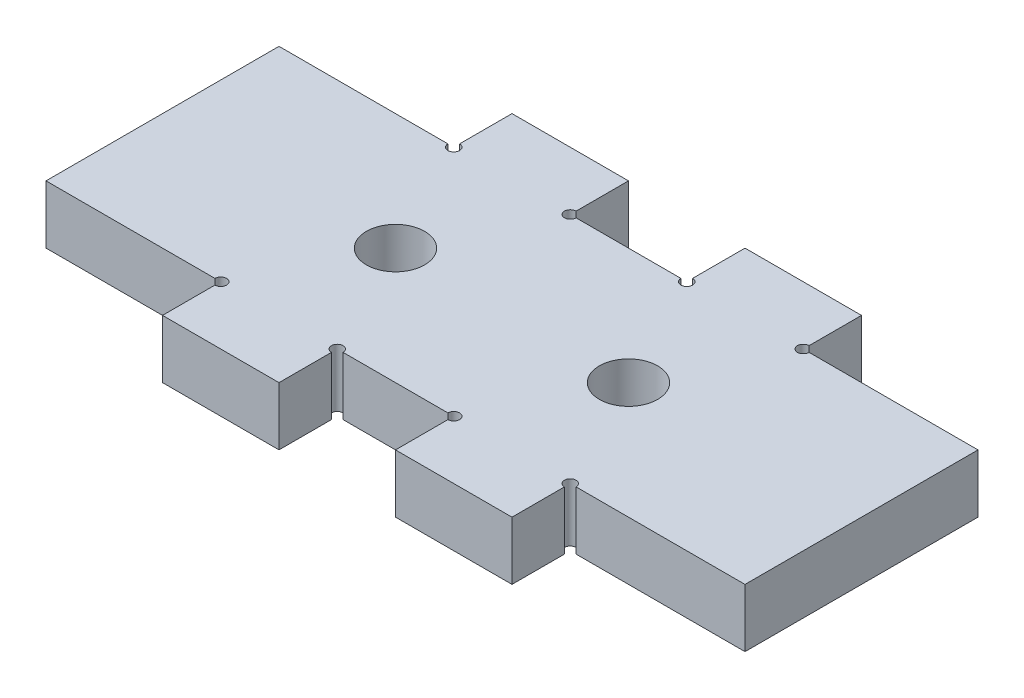
SolidWorks part; units mm, degrees
material "Acrylic (Medium-high impact)"
ref_plane "Front Plane" through (0, 0, 0) normal (0, 0, 1) x (1, 0, 0)
ref_plane "Top Plane" through (0, 0, 0) normal (0, 1, 0) x (1, 0, 0)
ref_plane "Right Plane" through (0, 0, 0) normal (1, 0, 0) x (0, 0, -1)
sketch "Sketch1" plane through (0, 0, 0) normal (0, 1, 0) x (1, 0, 0)
  line L0 (-19.05, 12.7) -> (-19.05, 19.05)
  line L1 (-38.1, 12.7) -> (-19.05, 12.7)
  line L2 (-38.1, 12.7) -> (-38.1, -12.7)
  line L3 (-38.1, -12.7) -> (-19.05, -12.7)
  line L4 (38.1, 12.7) -> (38.1, -12.7)
  line L5 (-38.1, 12.7) -> (38.1, -12.7) construction
  line L6 (-38.1, -12.7) -> (38.1, 12.7) construction
  line L7 (-19.05, 19.05) -> (-6.35, 19.05)
  line L8 (-6.35, 19.05) -> (-6.35, 12.7)
  line L9 (-6.35, 12.7) -> (6.35, 12.7)
  line L10 (0, -4.7893) -> (0, 19.05) construction
  line L11 (6.35, 19.05) -> (6.35, 12.7)
  line L12 (19.05, 19.05) -> (6.35, 19.05)
  line L13 (19.05, 12.7) -> (19.05, 19.05)
  line L14 (-8.6907, 0) -> (8.2657, 0) construction
  line L15 (-6.35, -19.05) -> (-6.35, -12.7)
  line L16 (-19.05, -19.05) -> (-6.35, -19.05)
  line L17 (-19.05, -12.7) -> (-19.05, -19.05)
  line L18 (19.05, -12.7) -> (19.05, -19.05)
  line L19 (19.05, -19.05) -> (6.35, -19.05)
  line L20 (6.35, -19.05) -> (6.35, -12.7)
  line L21 (19.05, 12.7) -> (38.1, 12.7)
  line L22 (19.05, -12.7) -> (38.1, -12.7)
  line L23 (-6.35, -12.7) -> (6.35, -12.7)
  point P0 (0, 0)
  dimension "D1" = 25.4
  dimension "D2" = 6.35
  dimension "D3" = 12.7
  dimension "D4" = 12.7
  dimension "D5" = 19.05
extrude "Boss-Extrude1" add sketch "Sketch1" along normal blind 6.35
sketch "Sketch2" plane through (0, 6.35, 0) normal (0, 1, 0) x (1, 0, 0)
  line L0 (-6.35, 19.05) -> (-19.05, 19.05) construction
  line L1 (19.05, 19.05) -> (6.35, 19.05) construction
  circle A0 centre (-12.7, 0) radius 3.175
  circle A1 centre (12.7, 0) radius 3.175
  point P7 (-12.7, 19.05)
  point P10 (12.7, 19.05)
  dimension "D1" = 6.35
  dimension "D2" = 6.35
extrude "Cut-Extrude1" cut sketch "Sketch2" against normal up to next
sketch "Sketch3" plane through (0, 6.35, 0) normal (0, 1, 0) x (1, 0, 0)
  point P0 (-19.05, 12.7)
  point P1 (-6.35, 12.7)
  point P3 (6.35, 12.7)
  point P5 (19.05, 12.7)
  point P7 (19.05, -12.7)
  point P9 (6.35, -12.7)
  point P11 (-6.35, -12.7)
  point P13 (-19.05, -12.7)
sketch "Sketch4" plane through (0, 6.35, 0) normal (0, 1, 0) x (1, 0, 0)
  circle A0 centre (-19.05, 12.7) radius 0.635
  dimension "D1" = 1.27
extrude "Cut-Extrude2" cut sketch "Sketch4" against normal up to next
pattern_sketch "Sketch-Pattern1" of "Cut-Extrude2" driven by "Sketch3"
sketch "Sketch5" plane through (0, 6.35, 0) normal (0, 1, 0) x (1, 0, 0)
  line L0 (-19.05, 0) -> (-6.35, 0) construction
  line L1 (-19.05, 3.175) -> (-6.35, 3.175)
  line L2 (-19.05, -3.175) -> (-6.35, -3.175)
  line L3 (0, 5.3719) -> (0, -5.695) construction
  line L4 (19.05, 0) -> (6.35, 0) construction
  line L5 (19.05, 3.175) -> (6.35, 3.175)
  line L6 (19.05, -3.175) -> (6.35, -3.175)
  arc A0 (-19.05, 3.175) -> (-19.05, -3.175) centre (-19.05, 0) ccw
  arc A1 (-6.35, -3.175) -> (-6.35, 3.175) centre (-6.35, 0) ccw
  circle A2 centre (-12.7, 0) radius 3.175 construction
  arc A3 (19.05, 3.175) -> (19.05, -3.175) centre (19.05, 0) cw
  arc A4 (6.35, -3.175) -> (6.35, 3.175) centre (6.35, 0) cw
  point P3 (-12.7, 0)
  point P14 (12.7, 0)
  dimension "D1" = 6.35
extrude "Cut-Extrude4" [suppressed] cut sketch "Sketch5" against normal up to next
